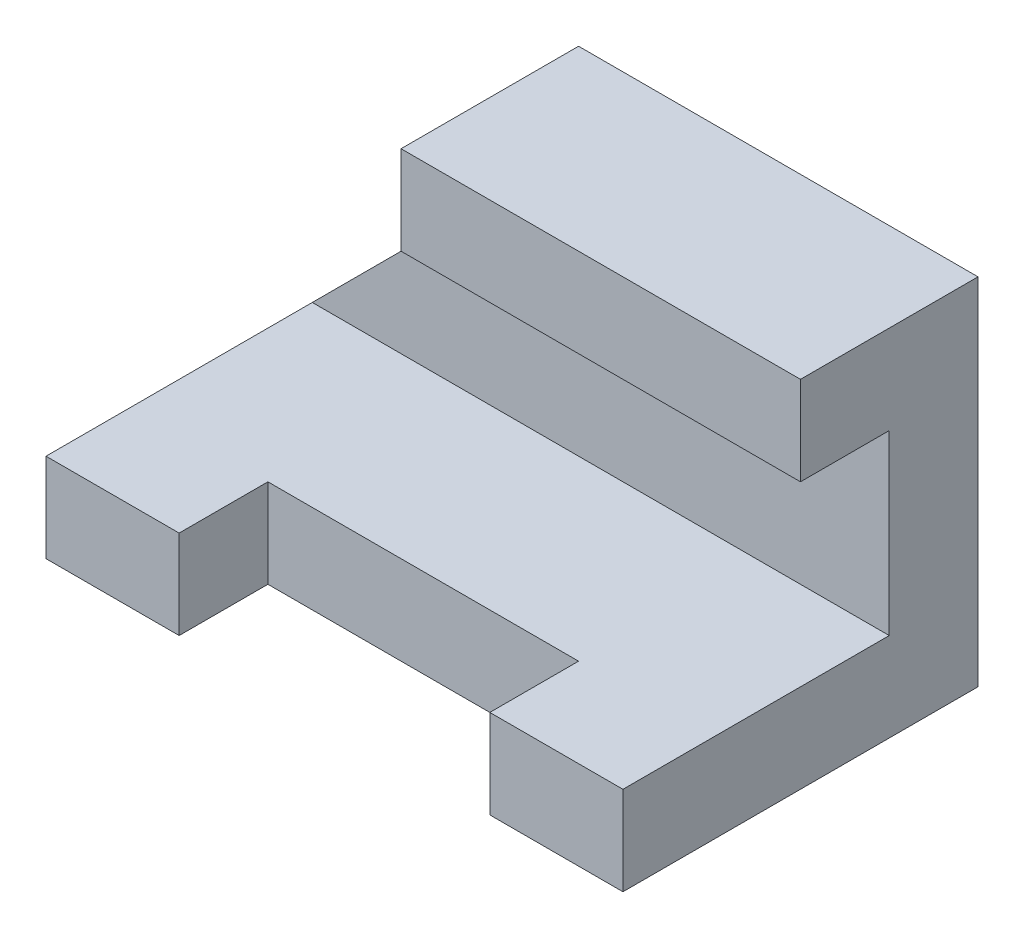
SolidWorks part; units mm, degrees
ref_plane "Front" through (0, 0, 0) normal (0, 0, 1) x (1, 0, 0)
ref_plane "Top" through (0, 0, 0) normal (0, 1, 0) x (1, 0, 0)
ref_plane "Right" through (0, 0, 0) normal (1, 0, 0) x (0, 0, -1)
sketch "Sketch1" plane through (0, 0, 0) normal (0, 0, 1) x (1, 0, 0)
  line L0 (0, 0) -> (13, 0)
  line L1 (13, 0) -> (13, 8)
  line L2 (13, 8) -> (4, 8)
  line L3 (4, 8) -> (4, 6)
  line L4 (4, 6) -> (0, 2)
  line L5 (0, 2) -> (0, 0)
  dimension "D1" = 8
  dimension "D2" = 9
  dimension "D3" = 2
  dimension "D4" = 13
  dimension "D5" = 2
extrude "Boss-Extrude1" add sketch "Sketch1" along normal blind 8
sketch "Sketch2" plane through (13, 0, 0) normal (1, 0, 0) x (0, 0, -1)
  line L0 (-8, 6) -> (0, 6) construction
  line L1 (-8, 8) -> (-4, 8)
  line L2 (-8, 8) -> (-8, 6)
  line L4 (-4, 8) -> (-4, 6)
  line L5 (-8, 2) -> (0, 2) construction
  line L6 (-4, 6) -> (-2, 6)
  line L7 (-8, 6) -> (-8, 2)
  line L8 (-8, 2) -> (-2, 2)
  line L9 (-2, 6) -> (-2, 2)
  dimension "D1" = 4
  dimension "D2" = 6
extrude "Cut-Extrude1" cut sketch "Sketch2" against normal blind 18
sketch "Sketch3" plane through (0, 2, 0) normal (0, 1, 0) x (1, 0, 0)
  line L0 (0, -8) -> (13, -8) construction
  line L1 (3, -8) -> (10, -8)
  line L2 (3, -8) -> (3, -6)
  line L3 (3, -6) -> (10, -6)
  line L4 (10, -8) -> (10, -6)
  line L5 (0, -8) -> (0, -2) construction
  line L6 (13, -8) -> (13, -2) construction
  dimension "D1" = 3
  dimension "D2" = 2
  dimension "D3" = 3
extrude "Cut-Extrude2" cut sketch "Sketch3" against normal blind 2
